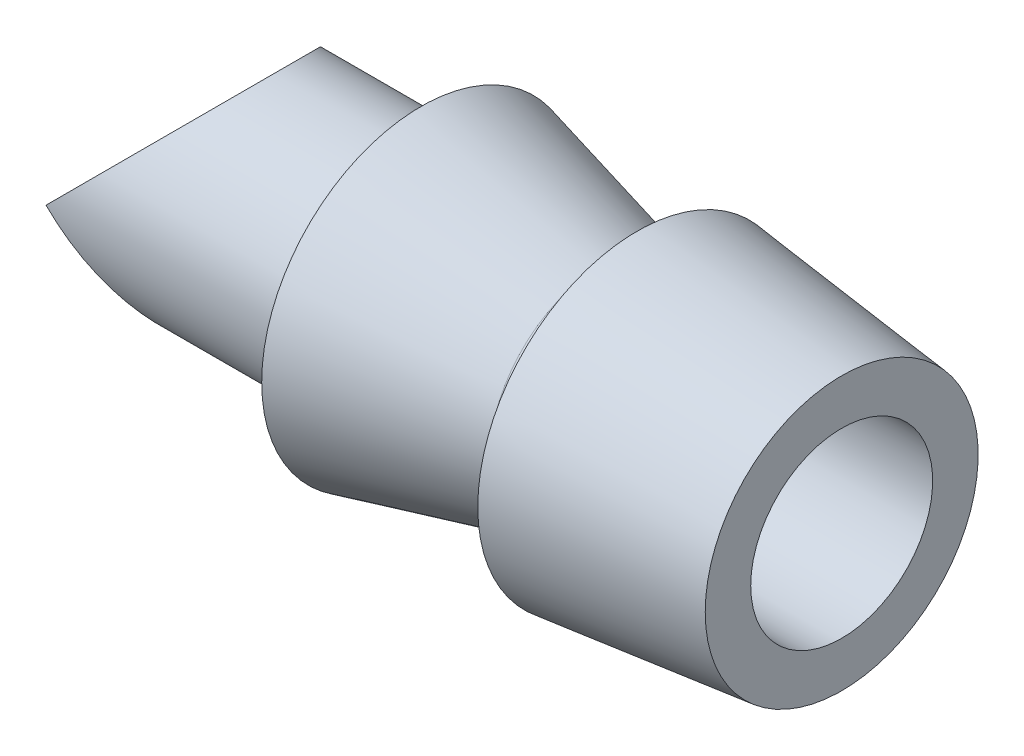
SolidWorks part; units mm, degrees
ref_plane "Front Plane" through (0, 0, 0) normal (0, 0, 1) x (1, 0, 0)
ref_plane "Top Plane" through (0, 0, 0) normal (0, 1, 0) x (1, 0, 0)
ref_plane "Right Plane" through (0, 0, 0) normal (1, 0, 0) x (0, 0, -1)
sketch "Sketch1" plane through (0, 0, 0) normal (0, 0, 1) x (1, 0, 0)
  line L0 (0, 0) -> (11.2819, 0) construction
  line L1 (10.637, 3) -> (6.137, 3.5)
  line L2 (-4.3547, 2) -> (10.637, 2)
  line L3 (-4.3547, 2) -> (-4.3547, 2.5)
  line L4 (-4.3547, 2.5) -> (1.387, 2.5)
  line L5 (10.637, 2) -> (10.637, 3)
  line L6 (6.137, 3.5) -> (6.137, 2.5)
  line L7 (5.387, 2.5) -> (1.387, 3.5)
  line L8 (1.387, 3.5) -> (1.387, 2.5)
  line L9 (5.387, 2.5) -> (6.137, 2.5)
  dimension "D1" = 2.5
  dimension "D2" = 1
  dimension "D3" = 15
  dimension "D4" = 4.5
  dimension "D5" = 4
  dimension "D6" = 1
  dimension "D7" = 1
  dimension "D8" = 0.75
  dimension "D9" = 2
revolve "Revolve1" add sketch "Sketch1" angle 360 about L0
sketch "Sketch2" plane through (0, 0, 0) normal (0, 0, 1) x (1, 0, 0)
  line L0 (-4.3547, 2.5) -> (-4.3547, -2.5) construction
  line L1 (-4.3547, 0) -> (-1.8547, 2.5)
  line L2 (1.387, 2.5) -> (-4.3547, 2.5) construction
  line L4 (-4.3547, -2.5) -> (1.387, -2.5) construction
  line L5 (-1.8547, -2.5) -> (-4.3547, 0)
  line L6 (-1.8547, 2.5) -> (-4.3547, 2.5)
  line L7 (-4.3547, 2.5) -> (-4.3547, 0)
  line L8 (-1.8547, -2.5) -> (-4.3547, -2.5)
  line L9 (-4.3547, -2.5) -> (-4.3547, 0)
  line L10 (-1.8547, -2.5) -> (-4.3547, 0)
  line L11 (-1.8547, 2.5) -> (-4.3547, 0)
extrude "Cut-Extrude3" cut sketch "Sketch2" against normal through all both and the other way through all contours L6 L7 L1 | L9 L8 L5
